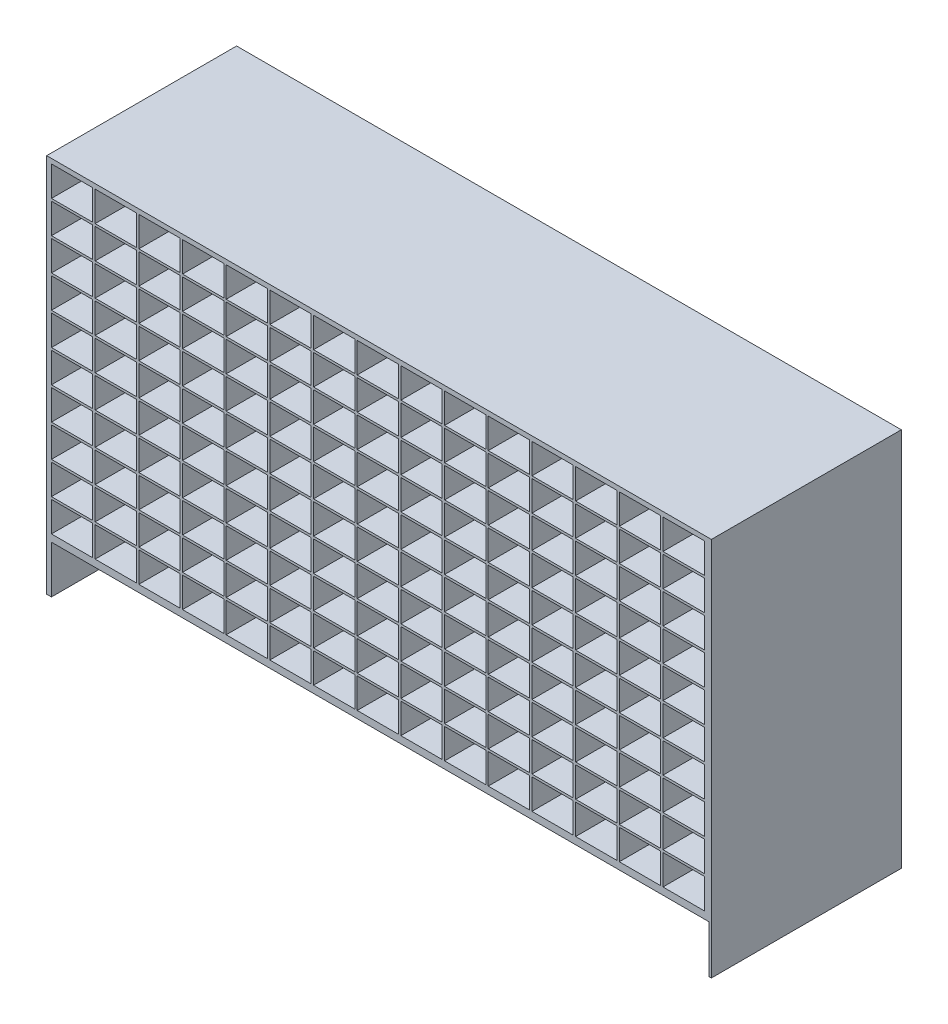
SolidWorks part; units mm, degrees
ref_plane "Alzado" through (0, 0, 0) normal (0, 0, 1) x (1, 0, 0)
ref_plane "Planta" through (0, 0, 0) normal (0, 1, 0) x (1, 0, 0)
ref_plane "Vista lateral" through (0, 0, 0) normal (1, 0, 0) x (0, 0, -1)
sketch "Croquis1" plane through (0, 0, 0) normal (0, 0, 1) x (1, 0, 0)
  line L1 (0, 0) -> (3500, 0)
  line L2 (0, 0) -> (0, 2000)
  line L3 (0, 2000) -> (3500, 2000)
  line L4 (3500, 0) -> (3500, 2000)
  dimension "D1" = 2000
  dimension "D2" = 3500
extrude "Saliente-Extruir1" add sketch "Croquis1" against normal blind 1000
sketch "Croquis2" plane through (0, 0, 0) normal (0, 0, 1) x (1, 0, 0)
  line L0 (3500, 0) -> (3500, 2000) construction
  line L1 (25, 0) -> (3487.5, 0)
  line L2 (0, 0) -> (0, 250) construction
  line L3 (25, 250) -> (3487.5, 250)
  line L9 (25, 250) -> (25, 0)
  line L11 (3500, 250) -> (3500, 0) construction
  line L13 (3487.5, 250) -> (3487.5, 0)
  dimension "D1" = 250
  dimension "D2" = 25
  dimension "D3" = 25
extrude "Cortar-Extruir1" cut sketch "Croquis2" against normal blind 975
sketch "Croquis3" plane through (0, 0, 0) normal (0, 0, 1) x (1, 0, 0)
  line L0 (0, 2000) -> (0, 0) construction
  line L1 (25, 1975) -> (3475, 1975) construction
  line L2 (25, 1975) -> (25, 275) construction
  line L3 (25, 275) -> (3475, 275) construction
  line L4 (3475, 1975) -> (3475, 275) construction
  line L5 (3500, 0) -> (3500, 2000) construction
  line L6 (3500, 2000) -> (0, 2000) construction
  line L7 (3487.5, 250) -> (25, 250) construction
  line L8 (255, 1975) -> (472.5, 1975)
  line L9 (25, 1975) -> (255, 1975) construction
  line L10 (25, 1975) -> (25, 1805) construction
  line L11 (25, 1805) -> (255, 1805) construction
  line L12 (255, 1975) -> (255, 1805) construction
  line L13 (25, 1975) -> (242.5, 1975)
  line L14 (25, 1975) -> (25, 1817.5)
  line L15 (25, 1817.5) -> (242.5, 1817.5)
  line L16 (242.5, 1975) -> (242.5, 1817.5)
  line L17 (255, 1975) -> (255, 1817.5)
  line L18 (255, 1817.5) -> (472.5, 1817.5)
  line L19 (472.5, 1975) -> (472.5, 1817.5)
  line L20 (485, 1975) -> (702.5, 1975)
  line L21 (485, 1975) -> (485, 1817.5)
  line L22 (485, 1817.5) -> (702.5, 1817.5)
  line L23 (702.5, 1975) -> (702.5, 1817.5)
  line L24 (715, 1975) -> (932.5, 1975)
  line L25 (715, 1975) -> (715, 1817.5)
  line L26 (715, 1817.5) -> (932.5, 1817.5)
  line L27 (932.5, 1975) -> (932.5, 1817.5)
  line L28 (945, 1975) -> (1162.5, 1975)
  line L29 (945, 1975) -> (945, 1817.5)
  line L30 (945, 1817.5) -> (1162.5, 1817.5)
  line L31 (1162.5, 1975) -> (1162.5, 1817.5)
  line L32 (1175, 1975) -> (1392.5, 1975)
  line L33 (1175, 1975) -> (1175, 1817.5)
  line L34 (1175, 1817.5) -> (1392.5, 1817.5)
  line L35 (1392.5, 1975) -> (1392.5, 1817.5)
  line L36 (1405, 1975) -> (1622.5, 1975)
  line L37 (1405, 1975) -> (1405, 1817.5)
  line L38 (1405, 1817.5) -> (1622.5, 1817.5)
  line L39 (1622.5, 1975) -> (1622.5, 1817.5)
  line L40 (1635, 1975) -> (1852.5, 1975)
  line L41 (1635, 1975) -> (1635, 1817.5)
  line L42 (1635, 1817.5) -> (1852.5, 1817.5)
  line L43 (1852.5, 1975) -> (1852.5, 1817.5)
  line L44 (1865, 1975) -> (2082.5, 1975)
  line L45 (1865, 1975) -> (1865, 1817.5)
  line L46 (1865, 1817.5) -> (2082.5, 1817.5)
  line L47 (2082.5, 1975) -> (2082.5, 1817.5)
  line L48 (2095, 1975) -> (2312.5, 1975)
  line L49 (2095, 1975) -> (2095, 1817.5)
  line L50 (2095, 1817.5) -> (2312.5, 1817.5)
  line L51 (2312.5, 1975) -> (2312.5, 1817.5)
  line L52 (2325, 1975) -> (2542.5, 1975)
  line L53 (2325, 1975) -> (2325, 1817.5)
  line L54 (2325, 1817.5) -> (2542.5, 1817.5)
  line L55 (2542.5, 1975) -> (2542.5, 1817.5)
  line L56 (2555, 1975) -> (2772.5, 1975)
  line L57 (2555, 1975) -> (2555, 1817.5)
  line L58 (2555, 1817.5) -> (2772.5, 1817.5)
  line L59 (2772.5, 1975) -> (2772.5, 1817.5)
  line L60 (2785, 1975) -> (3002.5, 1975)
  line L61 (2785, 1975) -> (2785, 1817.5)
  line L62 (2785, 1817.5) -> (3002.5, 1817.5)
  line L63 (3002.5, 1975) -> (3002.5, 1817.5)
  line L64 (3015, 1975) -> (3232.5, 1975)
  line L65 (3015, 1975) -> (3015, 1817.5)
  line L66 (3015, 1817.5) -> (3232.5, 1817.5)
  line L67 (3232.5, 1975) -> (3232.5, 1817.5)
  line L68 (3245, 1975) -> (3462.5, 1975)
  line L69 (3245, 1975) -> (3245, 1817.5)
  line L70 (3245, 1817.5) -> (3462.5, 1817.5)
  line L71 (3462.5, 1975) -> (3462.5, 1817.5)
  line L72 (255, 1805) -> (472.5, 1805)
  line L73 (255, 1805) -> (255, 1647.5)
  line L74 (255, 1647.5) -> (472.5, 1647.5)
  line L75 (472.5, 1805) -> (472.5, 1647.5)
  line L76 (485, 1805) -> (702.5, 1805)
  line L77 (485, 1805) -> (485, 1647.5)
  line L78 (485, 1647.5) -> (702.5, 1647.5)
  line L79 (702.5, 1805) -> (702.5, 1647.5)
  line L80 (715, 1805) -> (932.5, 1805)
  line L81 (715, 1805) -> (715, 1647.5)
  line L82 (715, 1647.5) -> (932.5, 1647.5)
  line L83 (932.5, 1805) -> (932.5, 1647.5)
  line L84 (945, 1805) -> (1162.5, 1805)
  line L85 (945, 1805) -> (945, 1647.5)
  line L86 (945, 1647.5) -> (1162.5, 1647.5)
  line L87 (1162.5, 1805) -> (1162.5, 1647.5)
  line L88 (1175, 1805) -> (1392.5, 1805)
  line L89 (1175, 1805) -> (1175, 1647.5)
  line L90 (1175, 1647.5) -> (1392.5, 1647.5)
  line L91 (1392.5, 1805) -> (1392.5, 1647.5)
  line L92 (1405, 1805) -> (1622.5, 1805)
  line L93 (1405, 1805) -> (1405, 1647.5)
  line L94 (1405, 1647.5) -> (1622.5, 1647.5)
  line L95 (1622.5, 1805) -> (1622.5, 1647.5)
  line L96 (1635, 1805) -> (1852.5, 1805)
  line L97 (1635, 1805) -> (1635, 1647.5)
  line L98 (1635, 1647.5) -> (1852.5, 1647.5)
  line L99 (1852.5, 1805) -> (1852.5, 1647.5)
  line L100 (1865, 1805) -> (2082.5, 1805)
  line L101 (1865, 1805) -> (1865, 1647.5)
  line L102 (1865, 1647.5) -> (2082.5, 1647.5)
  line L103 (2082.5, 1805) -> (2082.5, 1647.5)
  line L104 (2095, 1805) -> (2312.5, 1805)
  line L105 (2095, 1805) -> (2095, 1647.5)
  line L106 (2095, 1647.5) -> (2312.5, 1647.5)
  line L107 (2312.5, 1805) -> (2312.5, 1647.5)
  line L108 (2325, 1805) -> (2542.5, 1805)
  line L109 (2325, 1805) -> (2325, 1647.5)
  line L110 (2325, 1647.5) -> (2542.5, 1647.5)
  line L111 (2542.5, 1805) -> (2542.5, 1647.5)
  line L112 (2555, 1805) -> (2772.5, 1805)
  line L113 (2555, 1805) -> (2555, 1647.5)
  line L114 (2555, 1647.5) -> (2772.5, 1647.5)
  line L115 (2772.5, 1805) -> (2772.5, 1647.5)
  line L116 (2785, 1805) -> (3002.5, 1805)
  line L117 (2785, 1805) -> (2785, 1647.5)
  line L118 (2785, 1647.5) -> (3002.5, 1647.5)
  line L119 (3002.5, 1805) -> (3002.5, 1647.5)
  line L120 (3015, 1805) -> (3232.5, 1805)
  line L121 (3015, 1805) -> (3015, 1647.5)
  line L122 (3015, 1647.5) -> (3232.5, 1647.5)
  line L123 (3232.5, 1805) -> (3232.5, 1647.5)
  line L124 (3245, 1805) -> (3462.5, 1805)
  line L125 (3245, 1805) -> (3245, 1647.5)
  line L126 (3245, 1647.5) -> (3462.5, 1647.5)
  line L127 (3462.5, 1805) -> (3462.5, 1647.5)
  line L128 (255, 1635) -> (472.5, 1635)
  line L129 (255, 1635) -> (255, 1477.5)
  line L130 (255, 1477.5) -> (472.5, 1477.5)
  line L131 (472.5, 1635) -> (472.5, 1477.5)
  line L132 (485, 1635) -> (702.5, 1635)
  line L133 (485, 1635) -> (485, 1477.5)
  line L134 (485, 1477.5) -> (702.5, 1477.5)
  line L135 (702.5, 1635) -> (702.5, 1477.5)
  line L136 (715, 1635) -> (932.5, 1635)
  line L137 (715, 1635) -> (715, 1477.5)
  line L138 (715, 1477.5) -> (932.5, 1477.5)
  line L139 (932.5, 1635) -> (932.5, 1477.5)
  line L140 (945, 1635) -> (1162.5, 1635)
  line L141 (945, 1635) -> (945, 1477.5)
  line L142 (945, 1477.5) -> (1162.5, 1477.5)
  line L143 (1162.5, 1635) -> (1162.5, 1477.5)
  line L144 (1175, 1635) -> (1392.5, 1635)
  line L145 (1175, 1635) -> (1175, 1477.5)
  line L146 (1175, 1477.5) -> (1392.5, 1477.5)
  line L147 (1392.5, 1635) -> (1392.5, 1477.5)
  line L148 (1405, 1635) -> (1622.5, 1635)
  line L149 (1405, 1635) -> (1405, 1477.5)
  line L150 (1405, 1477.5) -> (1622.5, 1477.5)
  line L151 (1622.5, 1635) -> (1622.5, 1477.5)
  line L152 (1635, 1635) -> (1852.5, 1635)
  line L153 (1635, 1635) -> (1635, 1477.5)
  line L154 (1635, 1477.5) -> (1852.5, 1477.5)
  line L155 (1852.5, 1635) -> (1852.5, 1477.5)
  line L156 (1865, 1635) -> (2082.5, 1635)
  line L157 (1865, 1635) -> (1865, 1477.5)
  line L158 (1865, 1477.5) -> (2082.5, 1477.5)
  line L159 (2082.5, 1635) -> (2082.5, 1477.5)
  line L160 (2095, 1635) -> (2312.5, 1635)
  line L161 (2095, 1635) -> (2095, 1477.5)
  line L162 (2095, 1477.5) -> (2312.5, 1477.5)
  line L163 (2312.5, 1635) -> (2312.5, 1477.5)
  line L164 (2325, 1635) -> (2542.5, 1635)
  line L165 (2325, 1635) -> (2325, 1477.5)
  line L166 (2325, 1477.5) -> (2542.5, 1477.5)
  line L167 (2542.5, 1635) -> (2542.5, 1477.5)
  line L168 (2555, 1635) -> (2772.5, 1635)
  line L169 (2555, 1635) -> (2555, 1477.5)
  line L170 (2555, 1477.5) -> (2772.5, 1477.5)
  line L171 (2772.5, 1635) -> (2772.5, 1477.5)
  line L172 (2785, 1635) -> (3002.5, 1635)
  line L173 (2785, 1635) -> (2785, 1477.5)
  line L174 (2785, 1477.5) -> (3002.5, 1477.5)
  line L175 (3002.5, 1635) -> (3002.5, 1477.5)
  line L176 (3015, 1635) -> (3232.5, 1635)
  line L177 (3015, 1635) -> (3015, 1477.5)
  line L178 (3015, 1477.5) -> (3232.5, 1477.5)
  line L179 (3232.5, 1635) -> (3232.5, 1477.5)
  line L180 (3245, 1635) -> (3462.5, 1635)
  line L181 (3245, 1635) -> (3245, 1477.5)
  line L182 (3245, 1477.5) -> (3462.5, 1477.5)
  line L183 (3462.5, 1635) -> (3462.5, 1477.5)
  line L184 (255, 1465) -> (472.5, 1465)
  line L185 (255, 1465) -> (255, 1307.5)
  line L186 (255, 1307.5) -> (472.5, 1307.5)
  line L187 (472.5, 1465) -> (472.5, 1307.5)
  line L188 (485, 1465) -> (702.5, 1465)
  line L189 (485, 1465) -> (485, 1307.5)
  line L190 (485, 1307.5) -> (702.5, 1307.5)
  line L191 (702.5, 1465) -> (702.5, 1307.5)
  line L192 (715, 1465) -> (932.5, 1465)
  line L193 (715, 1465) -> (715, 1307.5)
  line L194 (715, 1307.5) -> (932.5, 1307.5)
  line L195 (932.5, 1465) -> (932.5, 1307.5)
  line L196 (945, 1465) -> (1162.5, 1465)
  line L197 (945, 1465) -> (945, 1307.5)
  line L198 (945, 1307.5) -> (1162.5, 1307.5)
  line L199 (1162.5, 1465) -> (1162.5, 1307.5)
  line L200 (1175, 1465) -> (1392.5, 1465)
  line L201 (1175, 1465) -> (1175, 1307.5)
  line L202 (1175, 1307.5) -> (1392.5, 1307.5)
  line L203 (1392.5, 1465) -> (1392.5, 1307.5)
  line L204 (1405, 1465) -> (1622.5, 1465)
  line L205 (1405, 1465) -> (1405, 1307.5)
  line L206 (1405, 1307.5) -> (1622.5, 1307.5)
  line L207 (1622.5, 1465) -> (1622.5, 1307.5)
  line L208 (1635, 1465) -> (1852.5, 1465)
  line L209 (1635, 1465) -> (1635, 1307.5)
  line L210 (1635, 1307.5) -> (1852.5, 1307.5)
  line L211 (1852.5, 1465) -> (1852.5, 1307.5)
  line L212 (1865, 1465) -> (2082.5, 1465)
  line L213 (1865, 1465) -> (1865, 1307.5)
  line L214 (1865, 1307.5) -> (2082.5, 1307.5)
  line L215 (2082.5, 1465) -> (2082.5, 1307.5)
  line L216 (2095, 1465) -> (2312.5, 1465)
  line L217 (2095, 1465) -> (2095, 1307.5)
  line L218 (2095, 1307.5) -> (2312.5, 1307.5)
  line L219 (2312.5, 1465) -> (2312.5, 1307.5)
  line L220 (2325, 1465) -> (2542.5, 1465)
  line L221 (2325, 1465) -> (2325, 1307.5)
  line L222 (2325, 1307.5) -> (2542.5, 1307.5)
  line L223 (2542.5, 1465) -> (2542.5, 1307.5)
  line L224 (2555, 1465) -> (2772.5, 1465)
  line L225 (2555, 1465) -> (2555, 1307.5)
  line L226 (2555, 1307.5) -> (2772.5, 1307.5)
  line L227 (2772.5, 1465) -> (2772.5, 1307.5)
  line L228 (2785, 1465) -> (3002.5, 1465)
  line L229 (2785, 1465) -> (2785, 1307.5)
  line L230 (2785, 1307.5) -> (3002.5, 1307.5)
  line L231 (3002.5, 1465) -> (3002.5, 1307.5)
  line L232 (3015, 1465) -> (3232.5, 1465)
  line L233 (3015, 1465) -> (3015, 1307.5)
  line L234 (3015, 1307.5) -> (3232.5, 1307.5)
  line L235 (3232.5, 1465) -> (3232.5, 1307.5)
  line L236 (3245, 1465) -> (3462.5, 1465)
  line L237 (3245, 1465) -> (3245, 1307.5)
  line L238 (3245, 1307.5) -> (3462.5, 1307.5)
  line L239 (3462.5, 1465) -> (3462.5, 1307.5)
  line L240 (255, 1295) -> (472.5, 1295)
  line L241 (255, 1295) -> (255, 1137.5)
  line L242 (255, 1137.5) -> (472.5, 1137.5)
  line L243 (472.5, 1295) -> (472.5, 1137.5)
  line L244 (485, 1295) -> (702.5, 1295)
  line L245 (485, 1295) -> (485, 1137.5)
  line L246 (485, 1137.5) -> (702.5, 1137.5)
  line L247 (702.5, 1295) -> (702.5, 1137.5)
  line L248 (715, 1295) -> (932.5, 1295)
  line L249 (715, 1295) -> (715, 1137.5)
  line L250 (715, 1137.5) -> (932.5, 1137.5)
  line L251 (932.5, 1295) -> (932.5, 1137.5)
  line L252 (945, 1295) -> (1162.5, 1295)
  line L253 (945, 1295) -> (945, 1137.5)
  line L254 (945, 1137.5) -> (1162.5, 1137.5)
  line L255 (1162.5, 1295) -> (1162.5, 1137.5)
  line L256 (1175, 1295) -> (1392.5, 1295)
  line L257 (1175, 1295) -> (1175, 1137.5)
  line L258 (1175, 1137.5) -> (1392.5, 1137.5)
  line L259 (1392.5, 1295) -> (1392.5, 1137.5)
  line L260 (1405, 1295) -> (1622.5, 1295)
  line L261 (1405, 1295) -> (1405, 1137.5)
  line L262 (1405, 1137.5) -> (1622.5, 1137.5)
  line L263 (1622.5, 1295) -> (1622.5, 1137.5)
  line L264 (1635, 1295) -> (1852.5, 1295)
  line L265 (1635, 1295) -> (1635, 1137.5)
  line L266 (1635, 1137.5) -> (1852.5, 1137.5)
  line L267 (1852.5, 1295) -> (1852.5, 1137.5)
  line L268 (1865, 1295) -> (2082.5, 1295)
  line L269 (1865, 1295) -> (1865, 1137.5)
  line L270 (1865, 1137.5) -> (2082.5, 1137.5)
  line L271 (2082.5, 1295) -> (2082.5, 1137.5)
  line L272 (2095, 1295) -> (2312.5, 1295)
  line L273 (2095, 1295) -> (2095, 1137.5)
  line L274 (2095, 1137.5) -> (2312.5, 1137.5)
  line L275 (2312.5, 1295) -> (2312.5, 1137.5)
  line L276 (2325, 1295) -> (2542.5, 1295)
  line L277 (2325, 1295) -> (2325, 1137.5)
  line L278 (2325, 1137.5) -> (2542.5, 1137.5)
  line L279 (2542.5, 1295) -> (2542.5, 1137.5)
  line L280 (2555, 1295) -> (2772.5, 1295)
  line L281 (2555, 1295) -> (2555, 1137.5)
  line L282 (2555, 1137.5) -> (2772.5, 1137.5)
  line L283 (2772.5, 1295) -> (2772.5, 1137.5)
  line L284 (2785, 1295) -> (3002.5, 1295)
  line L285 (2785, 1295) -> (2785, 1137.5)
  line L286 (2785, 1137.5) -> (3002.5, 1137.5)
  line L287 (3002.5, 1295) -> (3002.5, 1137.5)
  line L288 (3015, 1295) -> (3232.5, 1295)
  line L289 (3015, 1295) -> (3015, 1137.5)
  line L290 (3015, 1137.5) -> (3232.5, 1137.5)
  line L291 (3232.5, 1295) -> (3232.5, 1137.5)
  line L292 (3245, 1295) -> (3462.5, 1295)
  line L293 (3245, 1295) -> (3245, 1137.5)
  line L294 (3245, 1137.5) -> (3462.5, 1137.5)
  line L295 (3462.5, 1295) -> (3462.5, 1137.5)
  line L296 (255, 1125) -> (472.5, 1125)
  line L297 (255, 1125) -> (255, 967.5)
  line L298 (255, 967.5) -> (472.5, 967.5)
  line L299 (472.5, 1125) -> (472.5, 967.5)
  line L300 (485, 1125) -> (702.5, 1125)
  line L301 (485, 1125) -> (485, 967.5)
  line L302 (485, 967.5) -> (702.5, 967.5)
  line L303 (702.5, 1125) -> (702.5, 967.5)
  line L304 (715, 1125) -> (932.5, 1125)
  line L305 (715, 1125) -> (715, 967.5)
  line L306 (715, 967.5) -> (932.5, 967.5)
  line L307 (932.5, 1125) -> (932.5, 967.5)
  line L308 (945, 1125) -> (1162.5, 1125)
  line L309 (945, 1125) -> (945, 967.5)
  line L310 (945, 967.5) -> (1162.5, 967.5)
  line L311 (1162.5, 1125) -> (1162.5, 967.5)
  line L312 (1175, 1125) -> (1392.5, 1125)
  line L313 (1175, 1125) -> (1175, 967.5)
  line L314 (1175, 967.5) -> (1392.5, 967.5)
  line L315 (1392.5, 1125) -> (1392.5, 967.5)
  line L316 (1405, 1125) -> (1622.5, 1125)
  line L317 (1405, 1125) -> (1405, 967.5)
  line L318 (1405, 967.5) -> (1622.5, 967.5)
  line L319 (1622.5, 1125) -> (1622.5, 967.5)
  line L320 (1635, 1125) -> (1852.5, 1125)
  line L321 (1635, 1125) -> (1635, 967.5)
  line L322 (1635, 967.5) -> (1852.5, 967.5)
  line L323 (1852.5, 1125) -> (1852.5, 967.5)
  line L324 (1865, 1125) -> (2082.5, 1125)
  line L325 (1865, 1125) -> (1865, 967.5)
  line L326 (1865, 967.5) -> (2082.5, 967.5)
  line L327 (2082.5, 1125) -> (2082.5, 967.5)
  line L328 (2095, 1125) -> (2312.5, 1125)
  line L329 (2095, 1125) -> (2095, 967.5)
  line L330 (2095, 967.5) -> (2312.5, 967.5)
  line L331 (2312.5, 1125) -> (2312.5, 967.5)
  line L332 (2325, 1125) -> (2542.5, 1125)
  line L333 (2325, 1125) -> (2325, 967.5)
  line L334 (2325, 967.5) -> (2542.5, 967.5)
  line L335 (2542.5, 1125) -> (2542.5, 967.5)
  line L336 (2555, 1125) -> (2772.5, 1125)
  line L337 (2555, 1125) -> (2555, 967.5)
  line L338 (2555, 967.5) -> (2772.5, 967.5)
  line L339 (2772.5, 1125) -> (2772.5, 967.5)
  line L340 (2785, 1125) -> (3002.5, 1125)
  line L341 (2785, 1125) -> (2785, 967.5)
  line L342 (2785, 967.5) -> (3002.5, 967.5)
  line L343 (3002.5, 1125) -> (3002.5, 967.5)
  line L344 (3015, 1125) -> (3232.5, 1125)
  line L345 (3015, 1125) -> (3015, 967.5)
  line L346 (3015, 967.5) -> (3232.5, 967.5)
  line L347 (3232.5, 1125) -> (3232.5, 967.5)
  line L348 (3245, 1125) -> (3462.5, 1125)
  line L349 (3245, 1125) -> (3245, 967.5)
  line L350 (3245, 967.5) -> (3462.5, 967.5)
  line L351 (3462.5, 1125) -> (3462.5, 967.5)
  line L352 (255, 955) -> (472.5, 955)
  line L353 (255, 955) -> (255, 797.5)
  line L354 (255, 797.5) -> (472.5, 797.5)
  line L355 (472.5, 955) -> (472.5, 797.5)
  line L356 (485, 955) -> (702.5, 955)
  line L357 (485, 955) -> (485, 797.5)
  line L358 (485, 797.5) -> (702.5, 797.5)
  line L359 (702.5, 955) -> (702.5, 797.5)
  line L360 (715, 955) -> (932.5, 955)
  line L361 (715, 955) -> (715, 797.5)
  line L362 (715, 797.5) -> (932.5, 797.5)
  line L363 (932.5, 955) -> (932.5, 797.5)
  line L364 (945, 955) -> (1162.5, 955)
  line L365 (945, 955) -> (945, 797.5)
  line L366 (945, 797.5) -> (1162.5, 797.5)
  line L367 (1162.5, 955) -> (1162.5, 797.5)
  line L368 (1175, 955) -> (1392.5, 955)
  line L369 (1175, 955) -> (1175, 797.5)
  line L370 (1175, 797.5) -> (1392.5, 797.5)
  line L371 (1392.5, 955) -> (1392.5, 797.5)
  line L372 (1405, 955) -> (1622.5, 955)
  line L373 (1405, 955) -> (1405, 797.5)
  line L374 (1405, 797.5) -> (1622.5, 797.5)
  line L375 (1622.5, 955) -> (1622.5, 797.5)
  line L376 (1635, 955) -> (1852.5, 955)
  line L377 (1635, 955) -> (1635, 797.5)
  line L378 (1635, 797.5) -> (1852.5, 797.5)
  line L379 (1852.5, 955) -> (1852.5, 797.5)
  line L380 (1865, 955) -> (2082.5, 955)
  line L381 (1865, 955) -> (1865, 797.5)
  line L382 (1865, 797.5) -> (2082.5, 797.5)
  line L383 (2082.5, 955) -> (2082.5, 797.5)
  line L384 (2095, 955) -> (2312.5, 955)
  line L385 (2095, 955) -> (2095, 797.5)
  line L386 (2095, 797.5) -> (2312.5, 797.5)
  line L387 (2312.5, 955) -> (2312.5, 797.5)
  line L388 (2325, 955) -> (2542.5, 955)
  line L389 (2325, 955) -> (2325, 797.5)
  line L390 (2325, 797.5) -> (2542.5, 797.5)
  line L391 (2542.5, 955) -> (2542.5, 797.5)
  line L392 (2555, 955) -> (2772.5, 955)
  line L393 (2555, 955) -> (2555, 797.5)
  line L394 (2555, 797.5) -> (2772.5, 797.5)
  line L395 (2772.5, 955) -> (2772.5, 797.5)
  line L396 (2785, 955) -> (3002.5, 955)
  line L397 (2785, 955) -> (2785, 797.5)
  line L398 (2785, 797.5) -> (3002.5, 797.5)
  line L399 (3002.5, 955) -> (3002.5, 797.5)
  line L400 (3015, 955) -> (3232.5, 955)
  line L401 (3015, 955) -> (3015, 797.5)
  line L402 (3015, 797.5) -> (3232.5, 797.5)
  line L403 (3232.5, 955) -> (3232.5, 797.5)
  line L404 (3245, 955) -> (3462.5, 955)
  line L405 (3245, 955) -> (3245, 797.5)
  line L406 (3245, 797.5) -> (3462.5, 797.5)
  line L407 (3462.5, 955) -> (3462.5, 797.5)
  line L408 (255, 785) -> (472.5, 785)
  line L409 (255, 785) -> (255, 627.5)
  line L410 (255, 627.5) -> (472.5, 627.5)
  line L411 (472.5, 785) -> (472.5, 627.5)
  line L412 (485, 785) -> (702.5, 785)
  line L413 (485, 785) -> (485, 627.5)
  line L414 (485, 627.5) -> (702.5, 627.5)
  line L415 (702.5, 785) -> (702.5, 627.5)
  line L416 (715, 785) -> (932.5, 785)
  line L417 (715, 785) -> (715, 627.5)
  line L418 (715, 627.5) -> (932.5, 627.5)
  line L419 (932.5, 785) -> (932.5, 627.5)
  line L420 (945, 785) -> (1162.5, 785)
  line L421 (945, 785) -> (945, 627.5)
  line L422 (945, 627.5) -> (1162.5, 627.5)
  line L423 (1162.5, 785) -> (1162.5, 627.5)
  line L424 (1175, 785) -> (1392.5, 785)
  line L425 (1175, 785) -> (1175, 627.5)
  line L426 (1175, 627.5) -> (1392.5, 627.5)
  line L427 (1392.5, 785) -> (1392.5, 627.5)
  line L428 (1405, 785) -> (1622.5, 785)
  line L429 (1405, 785) -> (1405, 627.5)
  line L430 (1405, 627.5) -> (1622.5, 627.5)
  line L431 (1622.5, 785) -> (1622.5, 627.5)
  line L432 (1635, 785) -> (1852.5, 785)
  line L433 (1635, 785) -> (1635, 627.5)
  line L434 (1635, 627.5) -> (1852.5, 627.5)
  line L435 (1852.5, 785) -> (1852.5, 627.5)
  line L436 (1865, 785) -> (2082.5, 785)
  line L437 (1865, 785) -> (1865, 627.5)
  line L438 (1865, 627.5) -> (2082.5, 627.5)
  line L439 (2082.5, 785) -> (2082.5, 627.5)
  line L440 (2095, 785) -> (2312.5, 785)
  line L441 (2095, 785) -> (2095, 627.5)
  line L442 (2095, 627.5) -> (2312.5, 627.5)
  line L443 (2312.5, 785) -> (2312.5, 627.5)
  line L444 (2325, 785) -> (2542.5, 785)
  line L445 (2325, 785) -> (2325, 627.5)
  line L446 (2325, 627.5) -> (2542.5, 627.5)
  line L447 (2542.5, 785) -> (2542.5, 627.5)
  line L448 (2555, 785) -> (2772.5, 785)
  line L449 (2555, 785) -> (2555, 627.5)
  line L450 (2555, 627.5) -> (2772.5, 627.5)
  line L451 (2772.5, 785) -> (2772.5, 627.5)
  line L452 (2785, 785) -> (3002.5, 785)
  line L453 (2785, 785) -> (2785, 627.5)
  line L454 (2785, 627.5) -> (3002.5, 627.5)
  line L455 (3002.5, 785) -> (3002.5, 627.5)
  line L456 (3015, 785) -> (3232.5, 785)
  line L457 (3015, 785) -> (3015, 627.5)
  line L458 (3015, 627.5) -> (3232.5, 627.5)
  line L459 (3232.5, 785) -> (3232.5, 627.5)
  line L460 (3245, 785) -> (3462.5, 785)
  line L461 (3245, 785) -> (3245, 627.5)
  line L462 (3245, 627.5) -> (3462.5, 627.5)
  line L463 (3462.5, 785) -> (3462.5, 627.5)
  line L464 (255, 615) -> (472.5, 615)
  line L465 (255, 615) -> (255, 457.5)
  line L466 (255, 457.5) -> (472.5, 457.5)
  line L467 (472.5, 615) -> (472.5, 457.5)
  line L468 (485, 615) -> (702.5, 615)
  line L469 (485, 615) -> (485, 457.5)
  line L470 (485, 457.5) -> (702.5, 457.5)
  line L471 (702.5, 615) -> (702.5, 457.5)
  line L472 (715, 615) -> (932.5, 615)
  line L473 (715, 615) -> (715, 457.5)
  line L474 (715, 457.5) -> (932.5, 457.5)
  line L475 (932.5, 615) -> (932.5, 457.5)
  line L476 (945, 615) -> (1162.5, 615)
  line L477 (945, 615) -> (945, 457.5)
  line L478 (945, 457.5) -> (1162.5, 457.5)
  line L479 (1162.5, 615) -> (1162.5, 457.5)
  line L480 (1175, 615) -> (1392.5, 615)
  line L481 (1175, 615) -> (1175, 457.5)
  line L482 (1175, 457.5) -> (1392.5, 457.5)
  line L483 (1392.5, 615) -> (1392.5, 457.5)
  line L484 (1405, 615) -> (1622.5, 615)
  line L485 (1405, 615) -> (1405, 457.5)
  line L486 (1405, 457.5) -> (1622.5, 457.5)
  line L487 (1622.5, 615) -> (1622.5, 457.5)
  line L488 (1635, 615) -> (1852.5, 615)
  line L489 (1635, 615) -> (1635, 457.5)
  line L490 (1635, 457.5) -> (1852.5, 457.5)
  line L491 (1852.5, 615) -> (1852.5, 457.5)
  line L492 (1865, 615) -> (2082.5, 615)
  line L493 (1865, 615) -> (1865, 457.5)
  line L494 (1865, 457.5) -> (2082.5, 457.5)
  line L495 (2082.5, 615) -> (2082.5, 457.5)
  line L496 (2095, 615) -> (2312.5, 615)
  line L497 (2095, 615) -> (2095, 457.5)
  line L498 (2095, 457.5) -> (2312.5, 457.5)
  line L499 (2312.5, 615) -> (2312.5, 457.5)
  line L500 (2325, 615) -> (2542.5, 615)
  line L501 (2325, 615) -> (2325, 457.5)
  line L502 (2325, 457.5) -> (2542.5, 457.5)
  line L503 (2542.5, 615) -> (2542.5, 457.5)
  line L504 (2555, 615) -> (2772.5, 615)
  line L505 (2555, 615) -> (2555, 457.5)
  line L506 (2555, 457.5) -> (2772.5, 457.5)
  line L507 (2772.5, 615) -> (2772.5, 457.5)
  line L508 (2785, 615) -> (3002.5, 615)
  line L509 (2785, 615) -> (2785, 457.5)
  line L510 (2785, 457.5) -> (3002.5, 457.5)
  line L511 (3002.5, 615) -> (3002.5, 457.5)
  line L512 (3015, 615) -> (3232.5, 615)
  line L513 (3015, 615) -> (3015, 457.5)
  line L514 (3015, 457.5) -> (3232.5, 457.5)
  line L515 (3232.5, 615) -> (3232.5, 457.5)
  line L516 (3245, 615) -> (3462.5, 615)
  line L517 (3245, 615) -> (3245, 457.5)
  line L518 (3245, 457.5) -> (3462.5, 457.5)
  line L519 (3462.5, 615) -> (3462.5, 457.5)
  line L520 (255, 445) -> (472.5, 445)
  line L521 (255, 445) -> (255, 287.5)
  line L522 (255, 287.5) -> (472.5, 287.5)
  line L523 (472.5, 445) -> (472.5, 287.5)
  line L524 (485, 445) -> (702.5, 445)
  line L525 (485, 445) -> (485, 287.5)
  line L526 (485, 287.5) -> (702.5, 287.5)
  line L527 (702.5, 445) -> (702.5, 287.5)
  line L528 (715, 445) -> (932.5, 445)
  line L529 (715, 445) -> (715, 287.5)
  line L530 (715, 287.5) -> (932.5, 287.5)
  line L531 (932.5, 445) -> (932.5, 287.5)
  line L532 (945, 445) -> (1162.5, 445)
  line L533 (945, 445) -> (945, 287.5)
  line L534 (945, 287.5) -> (1162.5, 287.5)
  line L535 (1162.5, 445) -> (1162.5, 287.5)
  line L536 (1175, 445) -> (1392.5, 445)
  line L537 (1175, 445) -> (1175, 287.5)
  line L538 (1175, 287.5) -> (1392.5, 287.5)
  line L539 (1392.5, 445) -> (1392.5, 287.5)
  line L540 (1405, 445) -> (1622.5, 445)
  line L541 (1405, 445) -> (1405, 287.5)
  line L542 (1405, 287.5) -> (1622.5, 287.5)
  line L543 (1622.5, 445) -> (1622.5, 287.5)
  line L544 (1635, 445) -> (1852.5, 445)
  line L545 (1635, 445) -> (1635, 287.5)
  line L546 (1635, 287.5) -> (1852.5, 287.5)
  line L547 (1852.5, 445) -> (1852.5, 287.5)
  line L548 (1865, 445) -> (2082.5, 445)
  line L549 (1865, 445) -> (1865, 287.5)
  line L550 (1865, 287.5) -> (2082.5, 287.5)
  line L551 (2082.5, 445) -> (2082.5, 287.5)
  line L552 (2095, 445) -> (2312.5, 445)
  line L553 (2095, 445) -> (2095, 287.5)
  line L554 (2095, 287.5) -> (2312.5, 287.5)
  line L555 (2312.5, 445) -> (2312.5, 287.5)
  line L556 (2325, 445) -> (2542.5, 445)
  line L557 (2325, 445) -> (2325, 287.5)
  line L558 (2325, 287.5) -> (2542.5, 287.5)
  line L559 (2542.5, 445) -> (2542.5, 287.5)
  line L560 (2555, 445) -> (2772.5, 445)
  line L561 (2555, 445) -> (2555, 287.5)
  line L562 (2555, 287.5) -> (2772.5, 287.5)
  line L563 (2772.5, 445) -> (2772.5, 287.5)
  line L564 (2785, 445) -> (3002.5, 445)
  line L565 (2785, 445) -> (2785, 287.5)
  line L566 (2785, 287.5) -> (3002.5, 287.5)
  line L567 (3002.5, 445) -> (3002.5, 287.5)
  line L568 (3015, 445) -> (3232.5, 445)
  line L569 (3015, 445) -> (3015, 287.5)
  line L570 (3015, 287.5) -> (3232.5, 287.5)
  line L571 (3232.5, 445) -> (3232.5, 287.5)
  line L572 (3245, 445) -> (3462.5, 445)
  line L573 (3245, 445) -> (3245, 287.5)
  line L574 (3245, 287.5) -> (3462.5, 287.5)
  line L575 (3462.5, 445) -> (3462.5, 287.5)
  line L576 (25, 1805) -> (242.5, 1805)
  line L577 (25, 1805) -> (25, 1647.5)
  line L578 (25, 1647.5) -> (242.5, 1647.5)
  line L579 (242.5, 1805) -> (242.5, 1647.5)
  line L580 (25, 1635) -> (242.5, 1635)
  line L581 (25, 1635) -> (25, 1477.5)
  line L582 (25, 1477.5) -> (242.5, 1477.5)
  line L583 (242.5, 1635) -> (242.5, 1477.5)
  line L584 (25, 1465) -> (242.5, 1465)
  line L585 (25, 1465) -> (25, 1307.5)
  line L586 (25, 1307.5) -> (242.5, 1307.5)
  line L587 (242.5, 1465) -> (242.5, 1307.5)
  line L588 (25, 1295) -> (242.5, 1295)
  line L589 (25, 1295) -> (25, 1137.5)
  line L590 (25, 1137.5) -> (242.5, 1137.5)
  line L591 (242.5, 1295) -> (242.5, 1137.5)
  line L592 (25, 1125) -> (242.5, 1125)
  line L593 (25, 1125) -> (25, 967.5)
  line L594 (25, 967.5) -> (242.5, 967.5)
  line L595 (242.5, 1125) -> (242.5, 967.5)
  line L596 (25, 955) -> (242.5, 955)
  line L597 (25, 955) -> (25, 797.5)
  line L598 (25, 797.5) -> (242.5, 797.5)
  line L599 (242.5, 955) -> (242.5, 797.5)
  line L600 (25, 785) -> (242.5, 785)
  line L601 (25, 785) -> (25, 627.5)
  line L602 (25, 627.5) -> (242.5, 627.5)
  line L603 (242.5, 785) -> (242.5, 627.5)
  line L604 (25, 615) -> (242.5, 615)
  line L605 (25, 615) -> (25, 457.5)
  line L606 (25, 457.5) -> (242.5, 457.5)
  line L607 (242.5, 615) -> (242.5, 457.5)
  line L608 (25, 445) -> (242.5, 445)
  line L609 (25, 445) -> (25, 287.5)
  line L610 (25, 287.5) -> (242.5, 287.5)
  line L611 (242.5, 445) -> (242.5, 287.5)
  dimension "D1" = 25
  dimension "D2" = 25
  dimension "D3" = 25
  dimension "D4" = 25
  dimension "D5" = 170
  dimension "D6" = 230
  dimension "D7" = 12.5
  dimension "D8" = 12.5
  dimension "D9" = 217.5
  dimension "D10" = 15
  dimension "D11" = 10
extrude "Cortar-Extruir2" cut sketch "Croquis3" against normal through all
